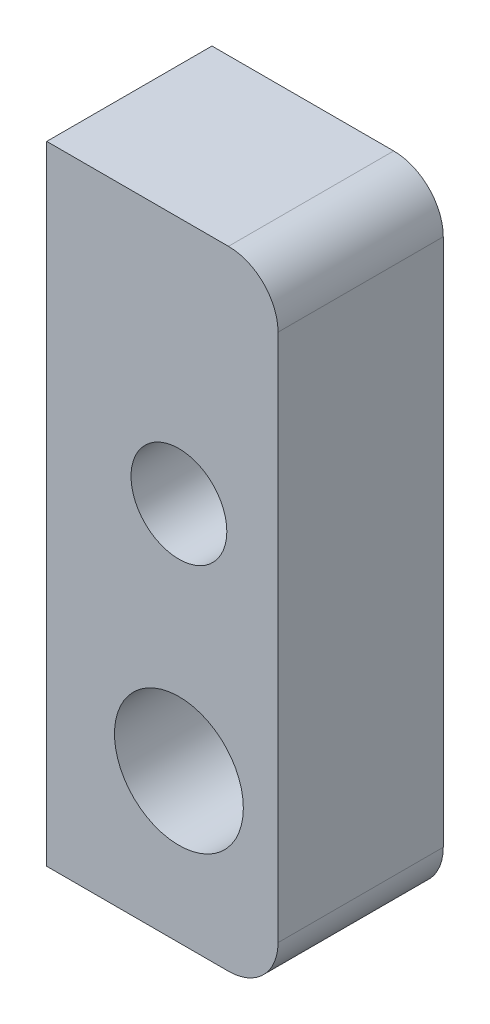
SolidWorks part; units mm, degrees
ref_plane "Front Plane" through (0, 0, 0) normal (0, 0, 1) x (1, 0, 0)
ref_plane "Top Plane" through (0, 0, 0) normal (0, 1, 0) x (1, 0, 0)
ref_plane "Right Plane" through (0, 0, 0) normal (1, 0, 0) x (0, 0, -1)
sketch "Sketch1" plane through (0, 0, 0) normal (0, 0, 1) x (1, 0, 0)
  line L0 (20, -9.5) -> (20, 9.5)
  line L1 (20, -9.5) -> (25.5, -9.5)
  line L2 (20, 9.5) -> (25.5, 9.5)
  line L3 (27, -8) -> (27, 8)
  line L4 (20, 0) -> (27, 0) construction
  line L5 (24, -9.5) -> (24, 9.5) construction
  circle A1 centre (24, -5) radius 1.95
  circle A2 centre (24, 2) radius 1.45
  arc A6 (25.5, -9.5) -> (27, -8) centre (25.5, -8) ccw
  arc A7 (25.5, 9.5) -> (27, 8) centre (25.5, 8) cw
  point P6 (0, 0)
  point P7 (24.2331, 1.8891)
  point P8 (0, 0)
  point P9 (24, -5)
  point P10 (24, 5)
  dimension "D2" = 2
  dimension "D3" = 1.3667
  dimension "D4" = 2.9
  dimension "D1" = 1.5
  dimension "D6" = 3.9
  dimension "D5" = 2.6333
  dimension "D7" = 5
extrude "Boss-Extrude2" add sketch "Sketch1" against normal blind 5
